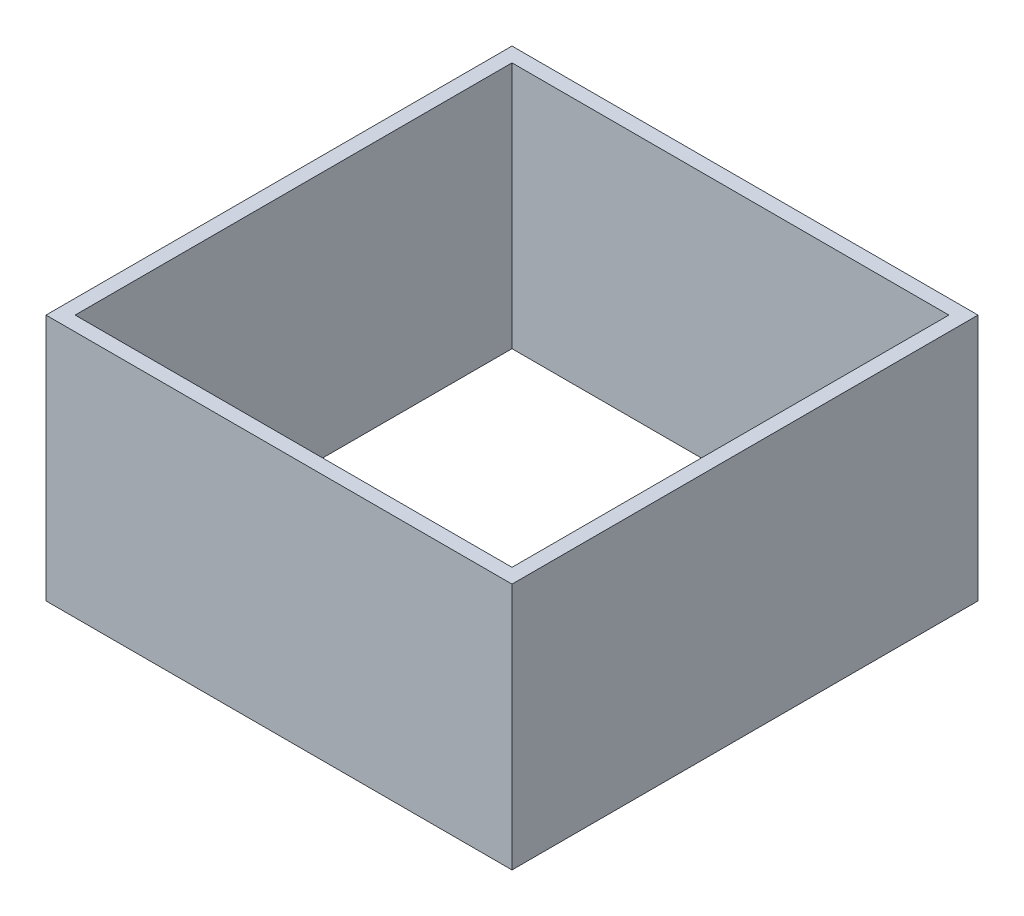
SolidWorks part; units mm, degrees
ref_plane "Front Plane" through (0, 0, 0) normal (0, 0, 1) x (1, 0, 0)
ref_plane "Top Plane" through (0, 0, 0) normal (0, 1, 0) x (1, 0, 0)
ref_plane "Right Plane" through (0, 0, 0) normal (1, 0, 0) x (0, 0, -1)
sketch "Sketch2" plane through (0, 0, 0) normal (0, 1, 0) x (1, 0, 0)
  line L1 (-50.8, 50.8) -> (50.8, 50.8)
  line L2 (-50.8, 50.8) -> (-50.8, -50.8)
  line L3 (-50.8, -50.8) -> (50.8, -50.8)
  line L4 (50.8, 50.8) -> (50.8, -50.8)
  line L5 (-50.8, 50.8) -> (50.8, -50.8) construction
  line L6 (-50.8, -50.8) -> (50.8, 50.8) construction
  line L7 (-47.625, 47.625) -> (47.625, 47.625)
  line L8 (-47.625, 47.625) -> (-47.625, -47.625)
  line L9 (-47.625, -47.625) -> (47.625, -47.625)
  line L10 (47.625, 47.625) -> (47.625, -47.625)
  line L11 (-47.625, 47.625) -> (47.625, -47.625) construction
  line L12 (-47.625, -47.625) -> (47.625, 47.625) construction
  point P0 (0, 0)
  point P6 (0, 0)
  dimension "D1" = 3.175
  dimension "D2" = 3.175
  dimension "D3" = 101.6
  dimension "D4" = 101.6
extrude "Boss-Extrude1" add sketch "Sketch2" along normal blind 53.975
